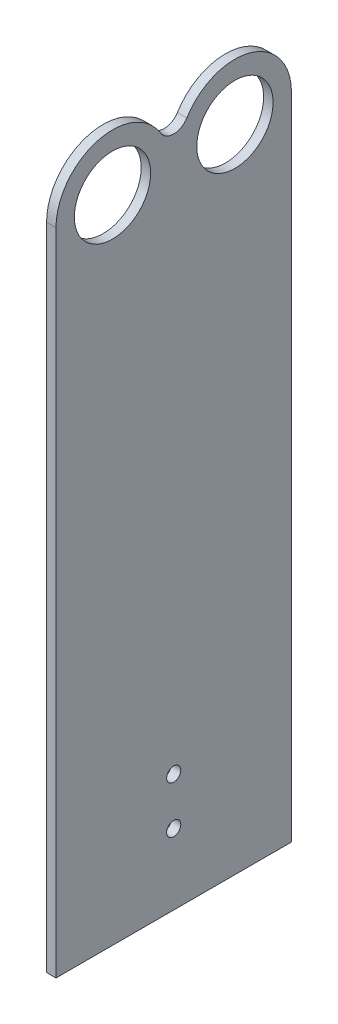
SolidWorks part; units mm, degrees
material "Acrylic (Medium-high impact)"
ref_plane "Front Plane" through (0, 0, 0) normal (0, 0, 1) x (1, 0, 0)
ref_plane "Top Plane" through (0, 0, 0) normal (0, 1, 0) x (1, 0, 0)
ref_plane "Right Plane" through (0, 0, 0) normal (1, 0, 0) x (0, 0, -1)
sketch "Sketch1" plane through (0, 0, 0) normal (0, 0, 1) x (1, 0, 0)
  line L0 (0, 35) -> (0, -115)
  line L4 (2, -115) -> (2, 35)
  line L5 (2, 35) -> (0, 35)
  line L6 (0, -115) -> (2, -115)
  point P9 (0, 0)
  dimension "D1" = 150
  dimension "D2" = 2
extrude "Boss-Extrude1" add sketch "Sketch1" along normal blind 50
sketch "Sketch3" plane through (2, 0, 0) normal (1, 0, 0) x (0, 0, -1)
  line L0 (-12, 35) -> (0, 35)
  line L1 (-50, 35) -> (0, 35) construction
  line L2 (0, -115) -> (0, 35) construction
  line L3 (-50, -115) -> (-50, 35) construction
  line L4 (-38, 35) -> (-50, 35)
  line L5 (-50, 35) -> (-50, 23)
  line L6 (0, 35) -> (0, 23)
  line L7 (-38, 35) -> (-12, 35)
  circle A0 centre (-38, 23) radius 8.1
  circle A1 centre (-12, 23) radius 8.1
  arc A2 (-27.7801, 29.2892) -> (-50, 23) centre (-38, 23) ccw
  arc A3 (0, 23) -> (-22.2199, 29.2892) centre (-12, 23) ccw
  arc A4 (-27.7801, 29.2892) -> (-22.2199, 29.2892) centre (-25, 31) ccw
  line M7 (0, -115) -> (0, 35)
  line M8 (0, 35) -> (-50, 35)
  line M9 (-50, 35) -> (-50, -115)
  dimension "D2" = 16.2
  dimension "D3" = 16.2
  dimension "D1" = 26
  dimension "D4" = 4
  dimension "D6" = 25
extrude "Cut-Extrude2" cut sketch "Sketch3" against normal blind 50 contours A1 | A0 | A2 M8 M9 | A2 A4 A3 M8 | A3 M7 M8
sketch "Sketch4" plane through (0, 0, 0) normal (-1, 0, 0) x (0, 0, 1)
  line L0 (25, -115) -> (25, 27.7357) construction
  line L1 (50, -115) -> (0, -115) construction
  arc A0 (22.2199, 29.2892) -> (27.7801, 29.2892) centre (25, 31) ccw construction
  circle A1 centre (25, -100) radius 1.5
  circle A2 centre (25, -90) radius 1.5
  dimension "D1" = 3
  dimension "D2" = 3
  dimension "D3" = 10
  dimension "D4" = 15
extrude "Cut-Extrude3" cut sketch "Sketch4" against normal through all both and the other way through all
